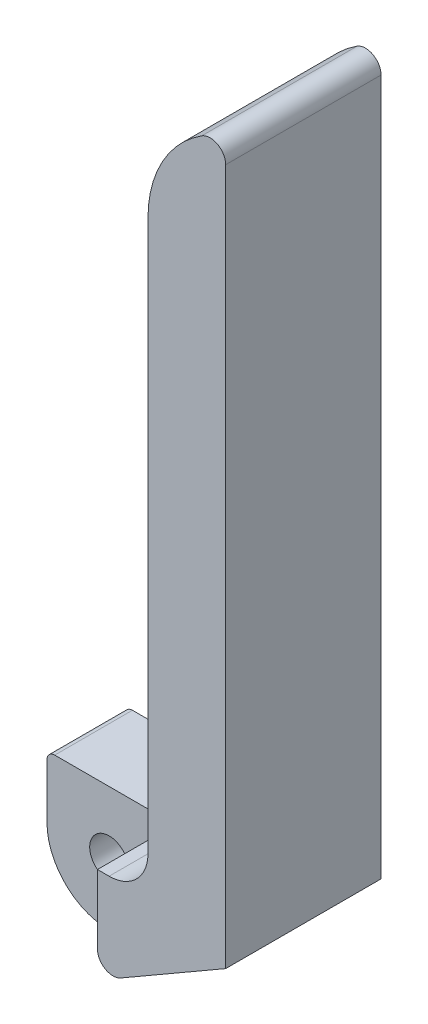
SolidWorks part; units mm, degrees
ref_plane "Front Plane" through (0, 0, 0) normal (0, 0, 1) x (1, 0, 0)
ref_plane "Top Plane" through (0, 0, 0) normal (0, 1, 0) x (1, 0, 0)
ref_plane "Right Plane" through (0, 0, 0) normal (1, 0, 0) x (0, 0, -1)
sketch "Sketch1" plane through (0, 0, 0) normal (0, 0, 1) x (1, 0, 0)
  line L0 (-7, 8) -> (10, 8)
  line L1 (15, 13) -> (15, 83.8579)
  line L2 (4, -6.9282) -> (25, 5.1962)
  line L3 (25, 5.1962) -> (25, 94.8123)
  line L4 (-8, 0) -> (-8, 7)
  circle A0 centre (0, 0) radius 2.5
  arc A1 (-8, 0) -> (4, -6.9282) centre (0, 0) ccw
  arc A2 (21.9231, 96.4976) -> (15, 83.8579) centre (30, 83.8579) ccw
  arc A3 (10, 8) -> (15, 13) centre (10, 13) ccw
  arc A4 (25, 94.8123) -> (21.9231, 96.4976) centre (23, 94.8123) ccw
  arc A5 (-7, 8) -> (-8, 7) centre (-7, 7) ccw
  point P14 (25, 98)
  dimension "D1" = 5
  dimension "D2" = 5
  dimension "D3" = 8
  dimension "D8" = 15
  dimension "D9" = 2
  dimension "D10" = 1
  dimension "D4" = 15
  dimension "D5" = 10
  dimension "D6" = 98
  dimension "D7" = 30
extrude "Boss-Extrude1" add sketch "Sketch1" along normal blind 20
sketch "Sketch2" plane through (0, 0, 20) normal (0, 0, 1) x (1, 0, 0)
  line L0 (8.5, 8) -> (8.5, -0.866)
  line L1 (10, 8) -> (-7, 8) construction
  line L2 (8.5, 8) -> (-7, 8)
  line L3 (4, -6.9282) -> (25, 5.1962) construction
  line L4 (4, -6.9282) -> (11.5, -2.5981)
  line L5 (-8, 7) -> (-8, 0) construction
  line L6 (-8, 7) -> (-8, 0)
  arc A1 (-8, 0) -> (4, -6.9282) centre (0, 0) ccw construction
  arc A2 (11.5, -2.5981) -> (8.5, -0.866) centre (10.5, -0.866) cw
  arc A3 (-7, 8) -> (-8, 7) centre (-7, 7) ccw construction
  arc A4 (-8, 0) -> (4, -6.9282) centre (0, 0) ccw
  arc A5 (-7, 8) -> (-8, 7) centre (-7, 7) ccw
  dimension "D2" = 2
  dimension "D1" = 8.5
extrude "Cut-Extrude1" cut sketch "Sketch2" against normal blind 10
